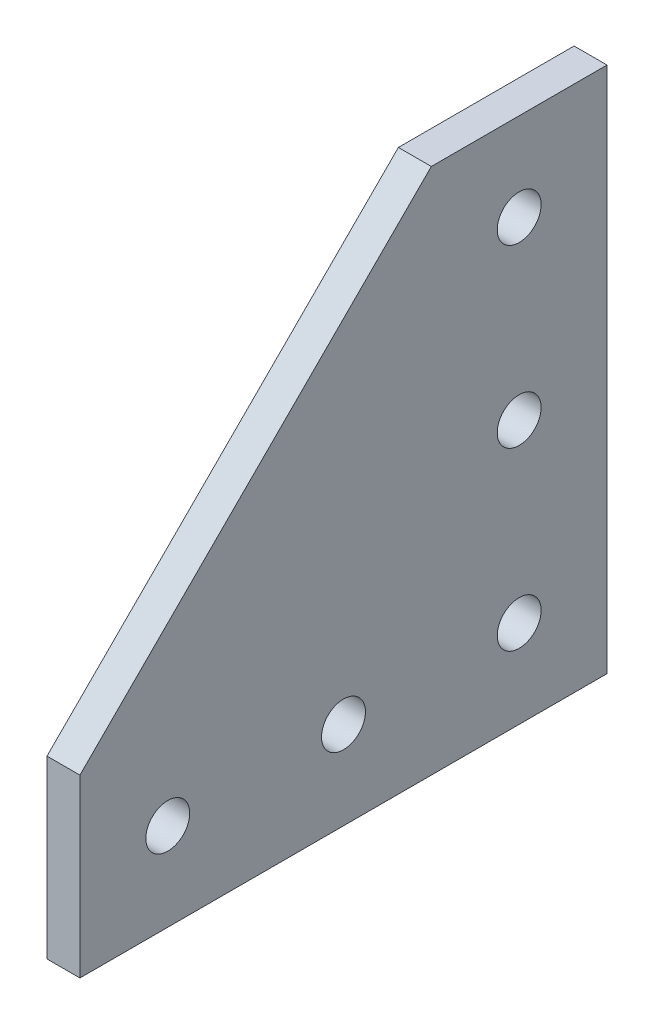
SolidWorks part; units mm, degrees
material "6061-T6 (SS)"
ref_plane "Front Plane" through (0, 0, 0) normal (0, 0, 1) x (1, 0, 0)
ref_plane "Top Plane" through (0, 0, 0) normal (0, 1, 0) x (1, 0, 0)
ref_plane "Right Plane" through (0, 0, 0) normal (1, 0, 0) x (0, 0, -1)
sketch "Sketch1" plane through (0, 0, 0) normal (1, 0, 0) x (0, 0, -1)
  line L0 (0, 0) -> (-76.2, 0)
  line L1 (-76.2, 0) -> (-76.2, 25.4)
  line L2 (-76.2, 25.4) -> (-25.4, 76.2)
  line L3 (-25.4, 76.2) -> (0, 76.2)
  line L4 (0, 76.2) -> (0, 0)
  line L5 (-76.2, 12.7) -> (0, 12.7) construction
  line L6 (-12.7, 76.2) -> (-12.7, 0) construction
  circle A0 centre (-12.7, 12.7) radius 3.175
  circle A1 centre (-12.7, 38.1) radius 3.175
  circle A2 centre (-12.7, 63.5) radius 3.175
  circle A3 centre (-38.1, 12.7) radius 3.175
  circle A4 centre (-63.5, 12.7) radius 3.175
  dimension "D3" = 6.35
  dimension "D1" = 25.4
  dimension "D2" = 76.2
  dimension "D4" = 12.7
  dimension "D5" = 12.7
extrude "Boss-Extrude1" add sketch "Sketch1" along normal blind 4.7625
